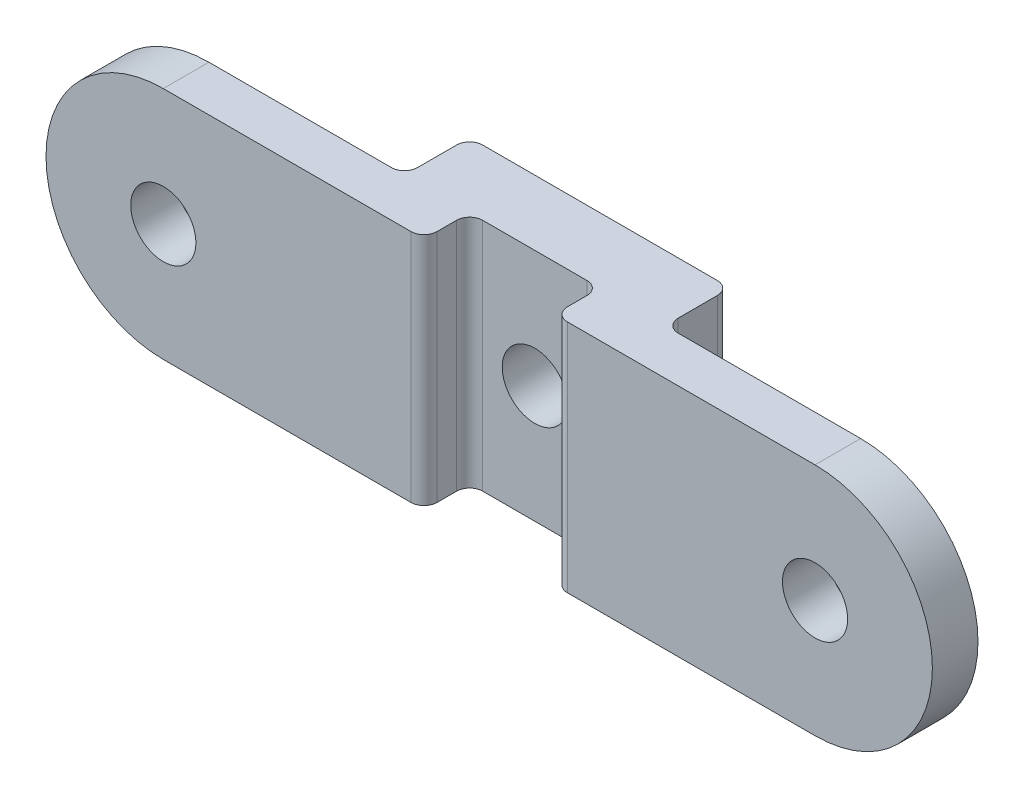
SolidWorks part; units mm, degrees
material "PLA"
ref_plane "Piano frontale" through (0, 0, 0) normal (0, 0, 1) x (1, 0, 0)
ref_plane "Piano superiore" through (0, 0, 0) normal (0, 1, 0) x (1, 0, 0)
ref_plane "Piano destro" through (0, 0, 0) normal (1, 0, 0) x (0, 0, -1)
sketch "Schizzo1" plane through (0, 0, 0) normal (0, 0, 1) x (1, 0, 0)
  line L1 (-10, -9) -> (10, -9)
  line L2 (-10, -9) -> (-10, 9)
  line L3 (-10, 9) -> (10, 9)
  line L4 (10, -9) -> (10, 9)
  line L5 (-10, -9) -> (10, 9) construction
  line L6 (-10, 9) -> (10, -9) construction
  circle A0 centre (0, 0) radius 2.5
  point P0 (0, 0)
  dimension "D2" = 5
  dimension "D1" = 20
  dimension "D3" = 18
extrude "Estrusione-Estrusione1" add sketch "Schizzo1" along normal blind 5
sketch "Schizzo2" plane through (0, -9, 0) normal (0, -1, 0) x (1, 0, 0)
  line L0 (0, 0) -> (0, 13.029) construction
  line L1 (-10, 0) -> (10, 0) construction
  line L2 (35, 8.5) -> (5, 8.5)
  line L3 (-35, 5) -> (-5, 5)
  line L4 (-35, 5) -> (-35, 8.5)
  line L5 (-35, 8.5) -> (-5, 8.5)
  line L6 (-5, 5) -> (-5, 8.5)
  line L7 (5, 5) -> (5, 8.5)
  line L8 (35, 5) -> (5, 5)
  line L9 (35, 5) -> (35, 8.5)
  line L11 (-10, 5) -> (-10, 0) construction
  line L12 (-10, 5) -> (10, 5) construction
  dimension "D1" = 3.5
  dimension "D2" = 5
  dimension "D3" = 30
extrude "Estrusione-Estrusione2" add sketch "Schizzo2" against normal through all
fillet "Raccordo2" radius 1 8 edges at (-5, 0, 8.5) (5, 0, 8.5) (-5, 0, 5) (5, 0, 5) (-10, 0, 0) (10, 0, 0) (10, 0, 5) (-10, 0, 5)
sketch "Schizzo3" plane through (0, 0, 8.5) normal (0, 0, 1) x (1, 0, 0)
  line L0 (-35, 0) -> (35, 0) construction
  line L1 (-35, 9) -> (-35, -9) construction
  line L2 (35, 9) -> (35, -9) construction
  line L3 (0, 0) -> (0, 9) construction
  line L4 (4, 9) -> (-4, 9) construction
  line L5 (25, 9) -> (25, -9) construction
  line L6 (25, 9) -> (35, 9)
  line L7 (35, 9) -> (35, -9)
  line L8 (35, -9) -> (25, -9)
  line L9 (-35, 9) -> (-35, -9)
  line L10 (-25, 9) -> (-35, 9)
  line L11 (-35, -9) -> (-25, -9)
  circle A0 centre (-25, 0) radius 2.5
  circle A1 centre (25, 0) radius 2.5
  arc A2 (25, -9) -> (25, 9) centre (25, 0) ccw
  arc A3 (-25, -9) -> (-25, 9) centre (-25, 0) cw
  dimension "D1" = 5
  dimension "D3" = 18
  dimension "D2" = 10
extrude "Taglio-Estrusione1" cut sketch "Schizzo3" against normal blind 10
